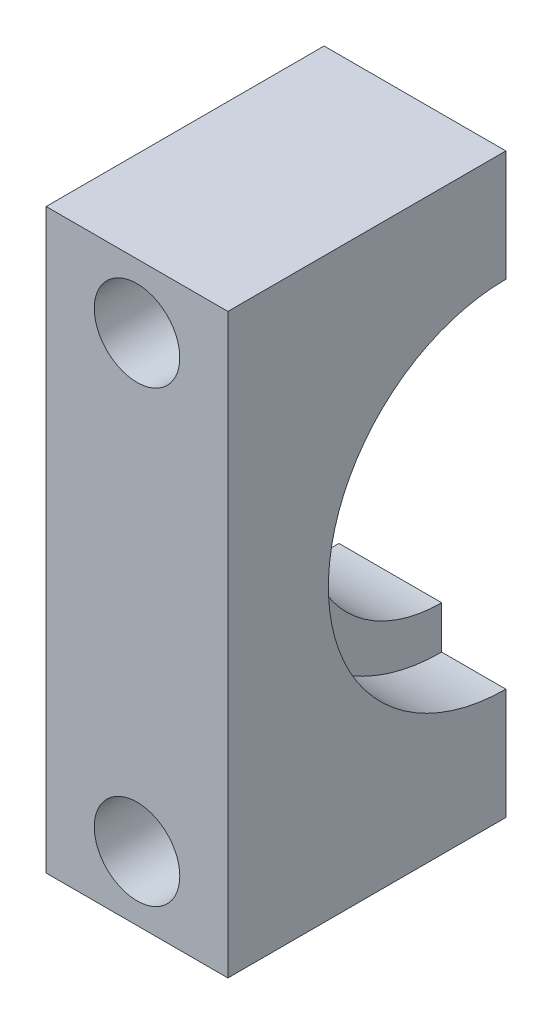
SolidWorks part; units mm, degrees
ref_plane "Front Plane" through (0, 0, 0) normal (0, 0, 1) x (1, 0, 0)
ref_plane "Top Plane" through (0, 0, 0) normal (0, 1, 0) x (1, 0, 0)
ref_plane "Right Plane" through (0, 0, 0) normal (1, 0, 0) x (0, 0, -1)
sketch "Esboço1" plane through (0, 0, 0) normal (0, 0, 1) x (1, 0, 0)
  line L1 (9, 188.9684) -> (9, 215.9684) construction
  line L3 (9, 188.9684) -> (0.5, 188.9684)
  line L4 (9, 188.9684) -> (9, 215.9684)
  line L5 (9, 215.9684) -> (0.5, 215.9684)
  line L6 (0.5, 215.9684) -> (0.5, 188.9684)
  dimension "D1" = 8.5
extrude "Ressalto-extrusão1" add sketch "Esboço1" along normal blind 13
sketch "Esboço3" plane through (9, 0, 0) normal (1, 0, 0) x (0, 0, -1)
  circle A2 centre (0, 202.4684) radius 8.3
  circle A3 centre (0, 202.4684) radius 8.3
  dimension "D1" = 0.3
extrude "Corte-extrusão1" cut sketch "Esboço3" against normal blind 3
sketch "Esboço4" plane through (6, 0, 0) normal (1, 0, 0) x (0, 0, -1)
  circle A2 centre (0, 202.4684) radius 6.3
  circle A3 centre (0, 202.4684) radius 6.3
  dimension "D1" = 0.3
extrude "Corte-extrusão2" cut sketch "Esboço4" against normal blind 5
sketch "Esboço7" plane through (0.5, 0, 0) normal (-1, 0, 0) x (0, 0, 1)
  circle A2 centre (0, 202.4684) radius 8.3
  circle A3 centre (0, 202.4684) radius 8.3
  dimension "D1" = 0.3
extrude "Corte-extrusão3" cut sketch "Esboço7" against normal blind 0.7
sketch "Esboço8" plane through (0, 0, 13) normal (0, 0, 1) x (1, 0, 0)
  line L0 (4.75, 188.9684) -> (4.75, 215.9684) construction
  line L1 (0.5, 188.9684) -> (9, 188.9684) construction
  line L2 (9, 215.9684) -> (0.5, 215.9684) construction
  line L3 (0.5, 202.4684) -> (9, 202.4684) construction
  line L4 (0.5, 215.9684) -> (0.5, 188.9684) construction
  line L5 (9, 188.9684) -> (9, 215.9684) construction
  circle A0 centre (4.75, 191.9684) radius 2
  circle A1 centre (4.75, 212.9684) radius 2
  point P14 (0, 0)
  dimension "D1" = 4
  dimension "D2" = 3
extrude "Corte-extrusão4" cut sketch "Esboço8" against normal through all
